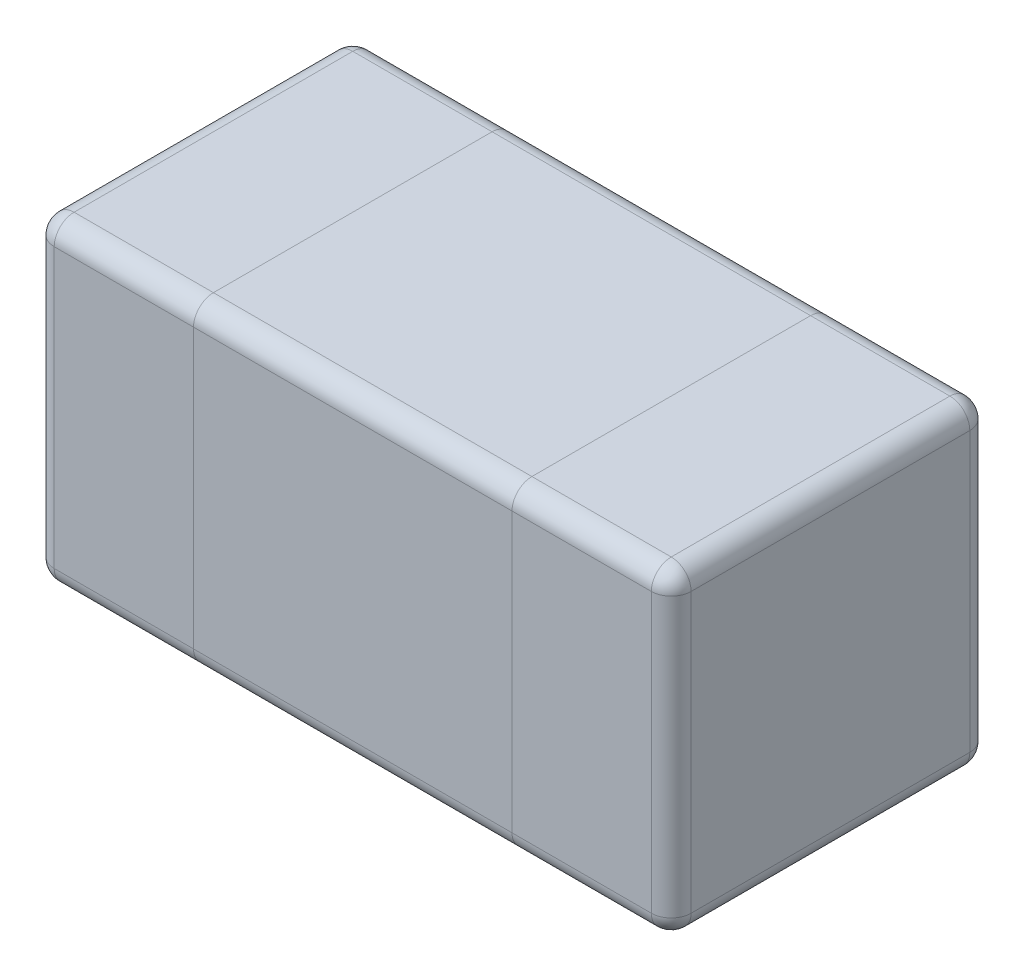
SolidWorks part; units mm, degrees
ref_plane "Front Plane" through (0, 0, 0) normal (0, 0, 1) x (1, 0, 0)
ref_plane "Top Plane" through (0, 0, 0) normal (0, 1, 0) x (1, 0, 0)
ref_plane "Right Plane" through (0, 0, 0) normal (1, 0, 0) x (0, 0, -1)
sketch "Sketch3" plane through (0, 0, 0) normal (0, 1, 0) x (1, 0, 0)
  line L1 (0, 0) -> (0.4, 0)
  line L2 (0, 0) -> (0, 0.8)
  line L3 (0, 0.8) -> (0.4, 0.8)
  line L4 (0.4, 0) -> (0.4, 0.8)
  line L5 (0.2, 0.8) -> (0.2, 0) construction
  line L6 (0, 0.4) -> (0.4, 0.4) construction
  line L7 (1.2, 0.8) -> (1.6, 0.8)
  line L8 (1.2, 0.8) -> (1.2, 0)
  line L9 (1.2, 0) -> (1.6, 0)
  line L10 (1.6, 0.8) -> (1.6, 0)
  line L11 (1.4, 0) -> (1.4, 0.8) construction
  line L12 (1.2, 0.4) -> (1.6, 0.4) construction
  point P100 (0.2, 0.4)
  point P138 (1.4, 0.4)
  dimension "D1" = 1.6
  dimension "D2" = 0.8
  dimension "D3" = 0.8
  dimension "D4" = 0.4
  dimension "D5" = 0.4
extrude "Boss-Extrude2" add sketch "Sketch3" along normal blind 0.8
sketch "Sketch4" plane through (0, 0, 0) normal (0, -1, 0) x (-1, 0, 0)
  line L1 (-0.4, 0.8) -> (-1.2, 0.8)
  line L2 (-0.4, 0.8) -> (-0.4, 0)
  line L3 (-0.4, 0) -> (-1.2, 0)
  line L4 (-1.2, 0.8) -> (-1.2, 0)
  line L5 (-0.8, 0) -> (-0.8, 0.8) construction
  line L6 (-0.4, 0.4) -> (-1.2, 0.4) construction
  point P164 (-0.8, 0.4)
extrude "Boss-Extrude3" add sketch "Sketch4" against normal blind 0.8 separate body
fillet "Fillet1" radius 0.05 8 edges at (0, 0.4, -0.8) (0, 0.8, -0.4) (0, 0.4, 0) (0, 0, -0.4) (0.2, 0.8, -0.8) (0.2, 0, -0.8) (0.2, 0, 0) (0.2, 0.8, 0)
fillet "Fillet2" radius 0.05 8 edges at (1.6, 0.4, 0) (1.6, 0.8, -0.4) (1.6, 0.4, -0.8) (1.6, 0, -0.4) (1.4, 0, 0) (1.4, 0, -0.8) (1.4, 0.8, 0) (1.4, 0.8, -0.8)
fillet "Fillet3" radius 0.05 4 edges at (0.8, 0, 0) (0.8, 0, -0.8) (0.8, 0.8, -0.8) (0.8, 0.8, 0)
sketch "Sketch5" [suppressed] plane through (0, 0.8, 0) normal (0, 1, 0) x (1, 0, 0)
  line L0 (0, 0.05) -> (0, 0.75) construction
  line L1 (0.4, 0.8) -> (1.2, 0.8) construction
  point P0 (0.8, 0.4)
  dimension "D1" = 0.8
  dimension "D2" = 0.4
